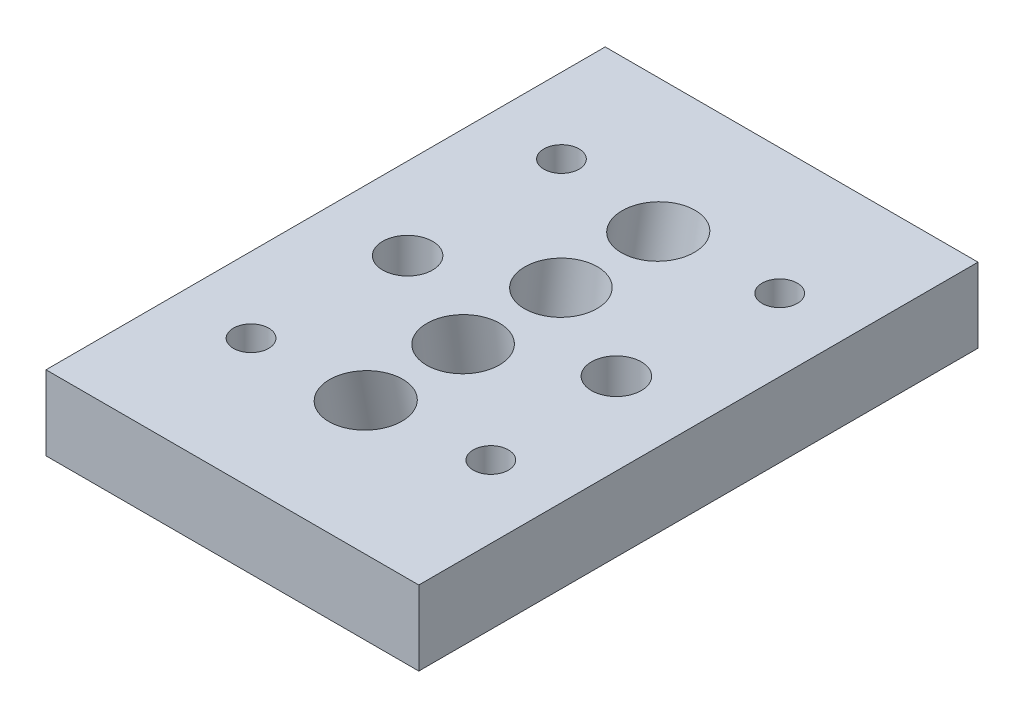
SolidWorks part; units mm, degrees
ref_plane "Front Plane" through (0, 0, 0) normal (0, 0, 1) x (1, 0, 0)
ref_plane "Top Plane" through (0, 0, 0) normal (0, 1, 0) x (1, 0, 0)
ref_plane "Right Plane" through (0, 0, 0) normal (1, 0, 0) x (0, 0, -1)
sketch "Sketch2" plane through (0, 0, 0) normal (0, 1, 0) x (1, 0, 0)
  line L1 (12.7, -19.05) -> (-12.7, -19.05)
  line L2 (12.7, -19.05) -> (12.7, 19.05)
  line L3 (12.7, 19.05) -> (-12.7, 19.05)
  line L4 (-12.7, -19.05) -> (-12.7, 19.05)
  line L5 (12.7, -19.05) -> (-12.7, 19.05) construction
  line L6 (12.7, 19.05) -> (-12.7, -19.05) construction
  point P0 (0, 0)
  dimension "D1" = 25.4
  dimension "D2" = 38.1
extrude "Boss-Extrude1" add sketch "Sketch2" along normal blind 5.08
sketch "Sketch6" plane through (12.7, 0, 0) normal (1, 0, 0) x (0, 0, -1)
  line L0 (-19.05, 124.7522) -> (-4.3561, 5.08) construction
  line L2 (-19.05, 5.08) -> (-19.05, 0) construction
  line L3 (-19.05, 5.08) -> (19.05, 5.08) construction
  line L4 (-4.3561, 5.08) -> (-4.3561, 22.1341) construction
  line L5 (-13.0683, 5.08) -> (-13.0683, 23.1616)
  line L6 (-13.0683, 5.08) -> (-16.6531, 23.776)
  dimension "D1" = 7
  dimension "D2" = 4.3561
  dimension "D3" = 5.9817
ref_plane "Plane3" through (12.7, 5.08, 4.3561) normal (0, -0.9925, -0.1219) x (-1, 0, 0)
sketch "Sketch7" plane through (12.7, 5.08, 4.3561) normal (0, -0.9925, -0.1219) x (-1, 0, 0)
  circle A0 centre (12.7, 1.016) radius 2.4638
extrude "Cut-Extrude1" cut sketch "Sketch7" along normal through all and the other way through all
ref_plane "Plane4" through (0, 0, 0) normal (0, 0, -1) x (-1, 0, 0)
ref_plane "Plane5" through (12.7, 5.08, 13.0683) normal (0, 0.9821, 0.1883) x (1, 0, 0)
sketch "Sketch16" plane through (12.7, 5.08, 13.0683) normal (0, 0.9821, 0.1883) x (1, 0, 0)
  circle A0 centre (-12.7, 3.048) radius 2.4638
extrude "Cut-Extrude2" cut sketch "Sketch16" against normal through all and the other way through all
mirror "Mirror2" about plane through (0, 0, 0) normal (0, 0, -1) of "Cut-Extrude1", "Cut-Extrude2"
hole_wizard "M3 Clearance Hole1" positions "Sketch21" profile "Sketch20" hole size "M3" standard "ANSI Metric"
sketch "Sketch21" plane through (0, 5.08, 0) normal (0, 1, 0) x (1, 0, 0)
  line L0 (2.794, 0) -> (-2.794, 0) construction
  line L1 (-12.7, 19.05) -> (-12.7, -19.05) construction
  line L2 (12.7, -19.05) -> (12.7, 19.05) construction
  point P0 (7.112, 0)
  point P4 (-7.112, 0)
  dimension "D1" = 5.588
  dimension "D2" = 5.588
sketch "Sketch20" plane through (7.112, 5.08, 0) normal (1, 0, 0) x (0, 0, 1)
  line L0 (0, 0) -> (0, 26.4215)
  line L1 (0, 26.4215) -> (1.7, 25.4)
  line L2 (1.7, 25.4) -> (1.7, 0)
  line L5 (1.7, 0) -> (0, 0)
  line L10 (0, 26.4215) -> (-1.7, 25.4) construction
  line L11 (0, -6.35) -> (0, 107.95) construction
  dimension "Hole Dia." = 3.4
  dimension "Hole Depth" = 25.4
  dimension "Drill Angle" = 118
sketch "Sketch17" plane through (0, 5.08, 0) normal (0, 1, 0) x (1, 0, 0)
  circle A0 centre (7.112, 0) radius 2.159
  circle A1 centre (-7.112, 0) radius 2.159
extrude "Cut-Extrude3" [suppressed] cut sketch "Sketch17" against normal through all
hole_wizard "M2 Clearance Hole1" positions "Sketch23" profile "Sketch22" hole size "M2" standard "ANSI Metric"
sketch "Sketch23" plane through (0, 5.08, 0) normal (0, 1, 0) x (1, 0, 0)
  point P0 (-7.5733, -10.2052)
  point P2 (-7.5733, 10.9429)
sketch "Sketch22" plane through (-7.5733, 5.08, 10.2052) normal (1, 0, 0) x (0, 0, 1)
  line L0 (0, 0) -> (0, 26.121)
  line L1 (0, 26.121) -> (1.2, 25.4)
  line L2 (1.2, 25.4) -> (1.2, 0)
  line L5 (1.2, 0) -> (0, 0)
  line L10 (0, 26.121) -> (-1.2, 25.4) construction
  line L11 (0, -6.35) -> (0, 107.95) construction
  dimension "Hole Dia." = 2.4
  dimension "Hole Depth" = 25.4
  dimension "Drill Angle" = 118
hole_wizard "M2 Clearance Hole2" positions "Sketch25" profile "Sketch24" hole size "M2" standard "ANSI Metric"
sketch "Sketch25" plane through (0, 5.08, 0) normal (0, 1, 0) x (1, 0, 0)
  point P0 (7.7797, -9.2219)
  point P2 (7.7797, 10.4576)
sketch "Sketch24" plane through (7.7797, 5.08, 9.2219) normal (1, 0, 0) x (0, 0, 1)
  line L0 (0, 0) -> (0, 26.121)
  line L1 (0, 26.121) -> (1.2, 25.4)
  line L2 (1.2, 25.4) -> (1.2, 0)
  line L5 (1.2, 0) -> (0, 0)
  line L10 (0, 26.121) -> (-1.2, 25.4) construction
  line L11 (0, -6.35) -> (0, 107.95) construction
  dimension "Hole Dia." = 2.4
  dimension "Hole Depth" = 25.4
  dimension "Drill Angle" = 118
